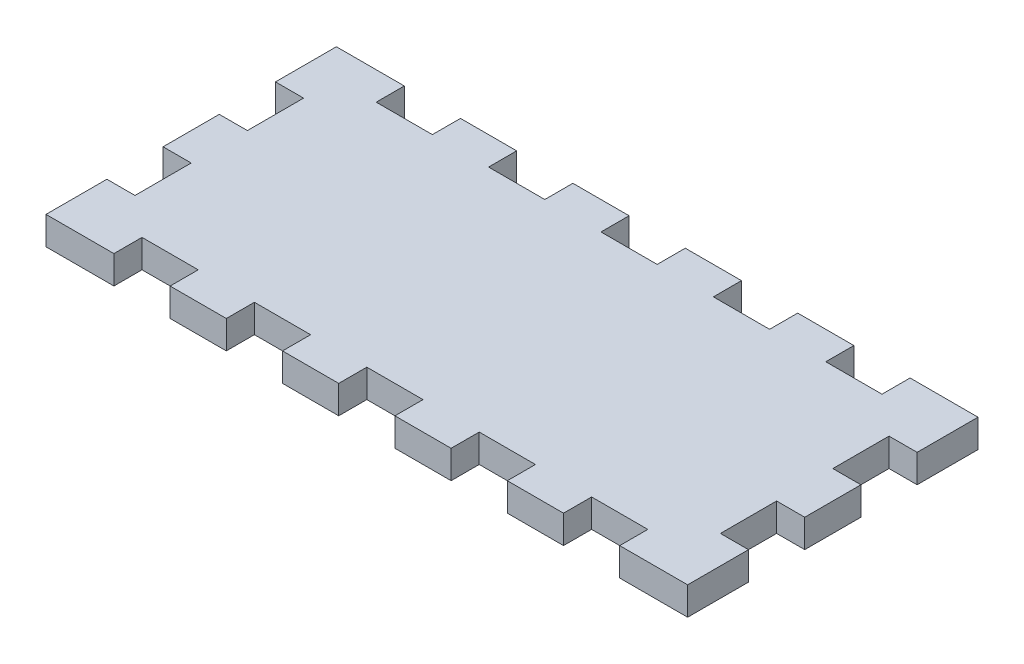
SolidWorks part; units mm, degrees
ref_plane "Front Plane" through (0, 0, 0) normal (0, 0, 1) x (1, 0, 0)
ref_plane "Top Plane" through (0, 0, 0) normal (0, 1, 0) x (1, 0, 0)
ref_plane "Right Plane" through (0, 0, 0) normal (1, 0, 0) x (0, 0, -1)
sketch "Sketch1" plane through (0, 0, 0) normal (0, 1, 0) x (1, 0, 0)
  line L1 (-54, -25) -> (-42, -25)
  line L3 (-54, 25) -> (-42, 25)
  line L5 (-66, 31) -> (-68.5, 31)
  line L6 (-68.5, 31) -> (-68.5, 18)
  line L7 (-66, 31) -> (-54, 31)
  line L8 (-54, 31) -> (-54, 25)
  line L9 (-42, 25) -> (-42, 31)
  line L10 (-42, 31) -> (-30, 31)
  line L11 (-30, 31) -> (-30, 25)
  line L12 (-18, 25) -> (-18, 31)
  line L13 (-18, 31) -> (-6, 31)
  line L14 (-6, 31) -> (-6, 25)
  line L15 (6, 25) -> (6, 31)
  line L16 (6, 31) -> (18, 31)
  line L17 (18, 31) -> (18, 25)
  line L18 (30, 25) -> (30, 31)
  line L19 (30, 31) -> (42, 31)
  line L20 (42, 31) -> (42, 25)
  line L21 (54, 25) -> (54, 31)
  line L22 (54, 31) -> (66, 31)
  line L24 (-55, 0) -> (55, 0) construction
  line L26 (54, -31) -> (66, -31)
  line L27 (54, -25) -> (54, -31)
  line L28 (42, -31) -> (42, -25)
  line L29 (30, -31) -> (42, -31)
  line L30 (30, -25) -> (30, -31)
  line L31 (18, -31) -> (18, -25)
  line L32 (6, -31) -> (18, -31)
  line L33 (6, -25) -> (6, -31)
  line L34 (-6, -31) -> (-6, -25)
  line L35 (-18, -31) -> (-6, -31)
  line L36 (-18, -25) -> (-18, -31)
  line L37 (-30, -31) -> (-30, -25)
  line L38 (-42, -31) -> (-30, -31)
  line L39 (-42, -25) -> (-42, -31)
  line L40 (-54, -31) -> (-54, -25)
  line L41 (-66, -31) -> (-54, -31)
  line L43 (-66, 18) -> (-62.5, 18)
  line L45 (-62.5, 6) -> (-66, 6)
  line L46 (-66, -6) -> (-62.5, -6)
  line L48 (-62.5, -18) -> (-66, -18)
  line L49 (0, -55) -> (0, 55) construction
  line L50 (62.5, -18) -> (66, -18)
  line L52 (66, -6) -> (62.5, -6)
  line L53 (62.5, 6) -> (66, 6)
  line L55 (66, 18) -> (62.5, 18)
  line L56 (-30, 25) -> (-18, 25)
  line L57 (-6, 25) -> (6, 25)
  line L58 (18, 25) -> (30, 25)
  line L59 (42, 25) -> (54, 25)
  line L62 (42, -25) -> (54, -25)
  line L63 (18, -25) -> (30, -25)
  line L64 (-30, -25) -> (-18, -25)
  line L65 (-6, -25) -> (6, -25)
  line L68 (-68.5, -31) -> (-66, -31)
  line L69 (-66, -18) -> (-68.5, -18)
  line L70 (-66, -6) -> (-68.5, -6)
  line L71 (-66, 6) -> (-68.5, 6)
  line L72 (-66, 18) -> (-68.5, 18)
  line L73 (-68.5, -18) -> (-68.5, -31)
  line L74 (-68.5, 6) -> (-68.5, -6)
  line L75 (68.5, 6) -> (68.5, -6)
  line L76 (68.5, -18) -> (68.5, -31)
  line L77 (66, 18) -> (68.5, 18)
  line L78 (66, 6) -> (68.5, 6)
  line L79 (66, -6) -> (68.5, -6)
  line L80 (66, -18) -> (68.5, -18)
  line L81 (68.5, -31) -> (66, -31)
  line L82 (68.5, 31) -> (68.5, 18)
  line L83 (66, 31) -> (68.5, 31)
  line L84 (66, 31) -> (66, 25) [skipped]
  line L85 (-62.5, -6) -> (-62.5, -18)
  line L86 (-62.5, 6) -> (-62.5, 18)
  line L87 (62.5, 18) -> (62.5, 6)
  line L88 (62.5, -6) -> (62.5, -18)
  point P0 (0, 0)
  point P82 (61.8989, -18)
  dimension "D3" = 6
  dimension "D4" = 12
  dimension "D8" = 7
  dimension "D5" = 6
  dimension "D9" = 2
extrude "Boss-Extrude1" add sketch "Sketch1" along normal blind 6
